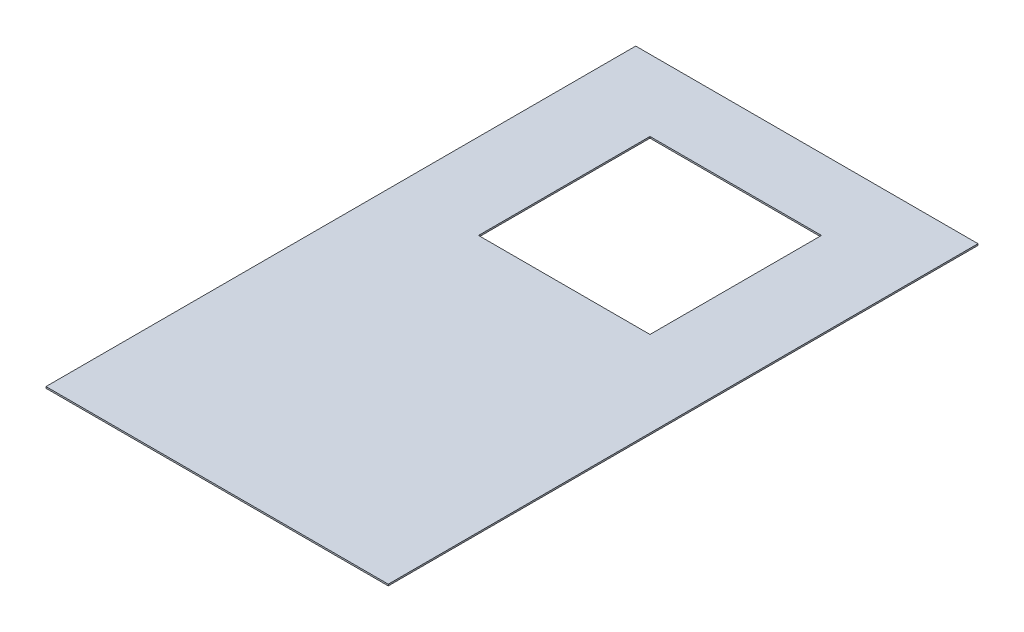
SolidWorks part; units mm, degrees
material "Oak"
ref_plane "Front Plane" through (0, 0, 0) normal (0, 0, 1) x (1, 0, 0)
ref_plane "Top Plane" through (0, 0, 0) normal (0, 1, 0) x (1, 0, 0)
ref_plane "Right Plane" through (0, 0, 0) normal (1, 0, 0) x (0, 0, -1)
sketch "Sketch1" plane through (0, 0, 0) normal (0, 1, 0) x (1, 0, 0)
  line L1 (-609.6, -1050.29) -> (609.6, -1050.29)
  line L2 (-609.6, -1050.29) -> (-609.6, 1050.29)
  line L3 (-609.6, 1050.29) -> (609.6, 1050.29)
  line L4 (609.6, -1050.29) -> (609.6, 1050.29)
  line L5 (-609.6, -1050.29) -> (609.6, 1050.29) construction
  line L6 (-609.6, 1050.29) -> (609.6, -1050.29) construction
  point P0 (0, 0)
  dimension "D1" = 1219.2
  dimension "D2" = 2100.58
extrude "Boss-Extrude1" add sketch "Sketch1" along normal blind 5.5562
sketch "Sketch2" plane through (0, 5.5562, 0) normal (0, 1, 0) x (1, 0, 0)
  line L1 (-305.435, 796.925) -> (305.435, 796.925)
  line L2 (-305.435, 796.925) -> (-305.435, 186.055)
  line L3 (-305.435, 186.055) -> (305.435, 186.055)
  line L4 (305.435, 796.925) -> (305.435, 186.055)
  line L5 (-305.435, 796.925) -> (305.435, 186.055) construction
  line L6 (-305.435, 186.055) -> (305.435, 796.925) construction
  circle A0 centre (0, 491.49) radius 254 construction
  point P0 (0, 491.49)
  point P5 (0, 0)
  dimension "D1" = 610.87
extrude "Cut-Extrude1" cut sketch "Sketch2" against normal through all both and the other way through all contours L1 L4 L3 L2
